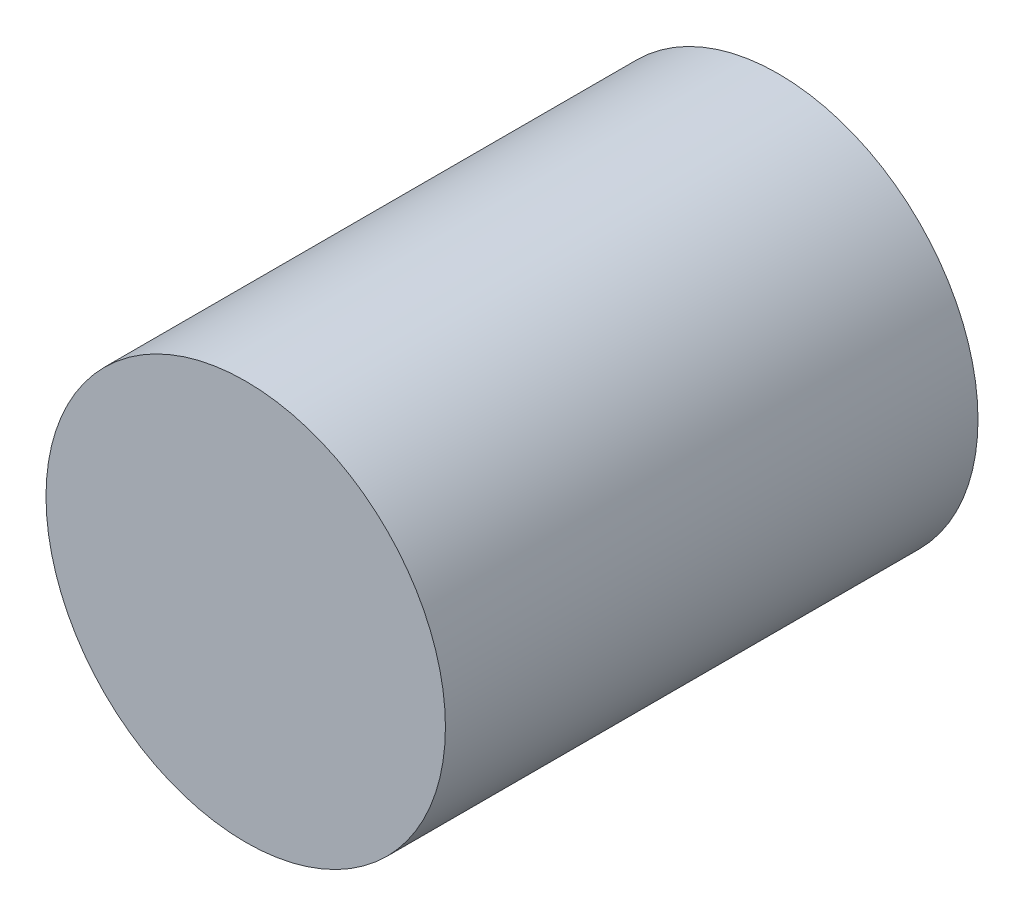
SolidWorks part; units mm, degrees
ref_plane "Front Plane" through (0, 0, 0) normal (0, 0, 1) x (1, 0, 0)
ref_plane "Top Plane" through (0, 0, 0) normal (0, 1, 0) x (1, 0, 0)
ref_plane "Right Plane" through (0, 0, 0) normal (1, 0, 0) x (0, 0, -1)
sketch "Sketch1" plane through (0, 0, 0) normal (0, 0, 1) x (1, 0, 0)
  circle A0 centre (0, 0) radius 1.905
  dimension "D1" = 3.81
extrude "Boss-Extrude1" add sketch "Sketch1" along normal blind 5.08
